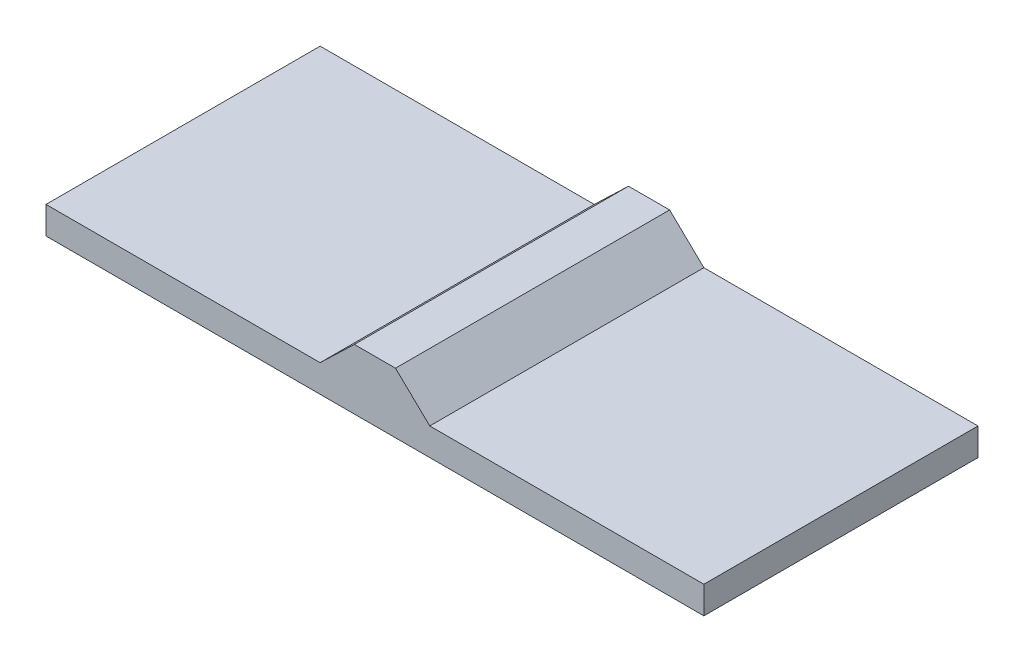
SolidWorks part; units mm, degrees
ref_plane "Front Plane" through (0, 0, 0) normal (0, 0, 1) x (1, 0, 0)
ref_plane "Top Plane" through (0, 0, 0) normal (0, 1, 0) x (1, 0, 0)
ref_plane "Right Plane" through (0, 0, 0) normal (1, 0, 0) x (0, 0, -1)
sketch "Sketch1" plane through (0, 0, 0) normal (0, 1, 0) x (1, 0, 0)
  line L1 (1800, -750) -> (-1800, -750)
  line L2 (1800, -750) -> (1800, 750)
  line L3 (1800, 750) -> (-1800, 750)
  line L4 (-1800, -750) -> (-1800, 750)
  line L5 (1800, -750) -> (-1800, 750) construction
  line L6 (1800, 750) -> (-1800, -750) construction
  point P0 (0, 0)
  dimension "D1" = 1500
  dimension "D2" = 3600
extrude "Boss-Extrude1" add sketch "Sketch1" along normal blind 150
sketch "Sketch3" plane through (0, 0, 750) normal (0, 0, 1) x (1, 0, 0)
  line L0 (0, 0) -> (0, 150) construction
  line L1 (-1800, 150) -> (1800, 150) construction
  line L2 (300, 150) -> (-300, 150)
  line L3 (-112.5, 330) -> (112.5, 330)
  line L4 (-300, 150) -> (-112.5, 330)
  line L5 (112.5, 330) -> (300, 150)
  point P5 (0, 330)
  point P8 (0, 150)
  dimension "D1" = 300
  dimension "D2" = 225
  dimension "D3" = 180
extrude "Boss-Extrude2" add sketch "Sketch3" along direction (0, 0, 1) on the side against the normal blind 1500
